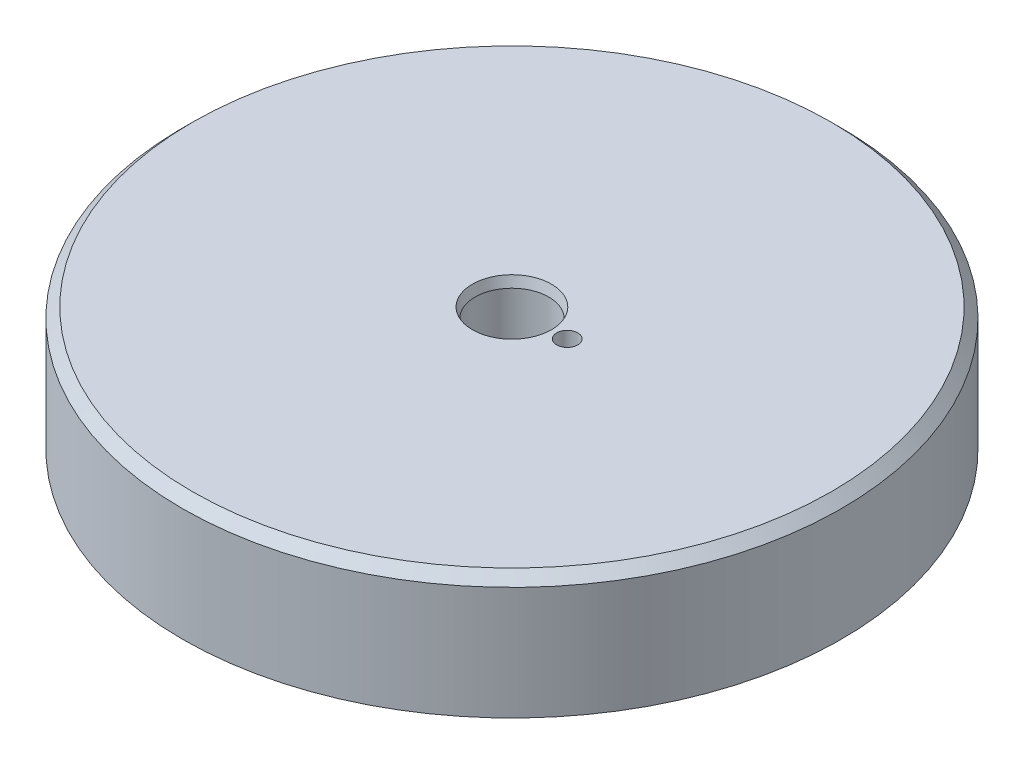
SolidWorks part; units mm, degrees
material "POM Acetal Copolymer"
ref_plane "Front Plane" through (0, 0, 0) normal (0, 0, 1) x (1, 0, 0)
ref_plane "Top Plane" through (0, 0, 0) normal (0, 1, 0) x (1, 0, 0)
ref_plane "Right Plane" through (0, 0, 0) normal (1, 0, 0) x (0, 0, -1)
ref_plane "Plane1" through (0, 0, 0) normal (0, -1, 0) x (1, 0, 0)
sketch "Sketch1" plane through (0, 0, 0) normal (0, -1, 0) x (1, 0, 0)
  circle A0 centre (0, 0) radius 42.545
  point P2 (0, 0)
  point P3 (0, 0)
  dimension "D1" = 85.09
extrude "Boss-Extrude1" add sketch "Sketch1" against normal blind 15.875
sketch "Sketch2" plane through (0, 0, 0) normal (0, -1, 0) x (1, 0, 0)
  circle A0 centre (0, 0) radius 39.3446
  circle A1 centre (0, 0) radius 34.7218
  point P3 (0, 0)
  point P4 (-3.2405, 12.0123)
  point P5 (0, 0)
  dimension "D1" = 69.4436
  dimension "D2" = 4.6228
extrude "Groove_232Oring" cut sketch "Sketch2" against normal blind 2.6416
sketch "Sketch9" plane through (0, 0, 0) normal (0, -1, 0) x (1, 0, 0)
  line L0 (7.3958, -27.6013) -> (-7.3958, 27.6013) construction
  line L1 (0, 0) -> (0, 28.575) construction
  circle A0 centre (0, 0) radius 28.575 construction
  point P6 (0, 0)
  point P7 (0, 28.575)
  dimension "D1" = 57.15
  dimension "D2" = 15
hole_wizard "1/4-20 Tapped Hole1" positions "Sketch11" profile "Sketch13" tap size "1/4-20" standard "ANSI Inch"
sketch "Sketch11" plane through (0, 0, 0) normal (0, -1, 0) x (-1, 0, 0)
  point P0 (-7.3958, 27.6013)
  point P3 (7.3958, -27.6013)
sketch "Sketch13" plane through (7.3958, 0, -27.6013) normal (1, 0, 0) x (0, 0, -1)
  line L0 (0, 0) -> (0, 9.4078)
  line L1 (0, 9.4078) -> (2.5527, 7.874)
  line L2 (2.5527, 7.874) -> (2.5527, 0)
  line L5 (2.5527, 0) -> (0, 0)
  line L10 (0, 9.4078) -> (-2.5527, 7.874) construction
  line L11 (0, -6.35) -> (0, 107.95) construction
  dimension "Tap Drill Dia." = 5.1054
  dimension "Tap Drill Depth" = 7.874
  dimension "Drill Angle" = 118
cosmetic thread "Hole Thread1" parameters "D1"=12.7, "D2"=6.35
cosmetic thread "Hole Thread2" parameters "D1"=12.7, "D2"=6.35
sketch "Sketch7" plane through (0, 15.875, 0) normal (0, 1, 0) x (-1, 0, 0)
  circle A0 centre (0, 0) radius 4.7625
  point P2 (0, 0)
  dimension "D1" = 9.525
extrude "Cut-Extrude2" cut sketch "Sketch7" against normal through all
sketch "Sketch8" plane through (0, 15.875, 0) normal (0, 1, 0) x (-1, 0, 0)
  line L0 (-7.1374, 0) -> (0, 0) construction
  circle A0 centre (-7.1374, 0) radius 1.3589
  dimension "D1" = 2.7178
  dimension "D2" = 7.1374
extrude "Cut-Extrude3" cut sketch "Sketch8" against normal blind 3.302
chamfer "Chamfer1" distance 0.3403 angle 75 1 edges at (0, 15.875, -4.7625)
chamfer "Chamfer2" distance 1.27 angle 45 1 edges at (0, 15.875, 42.545)
fillet "Fillet1" radius 0.254 4 edges at (0, 0, 34.7218) (0, 2.6416, 34.7218) (0, 2.6416, 39.3446) (0, 0, 39.3446)
